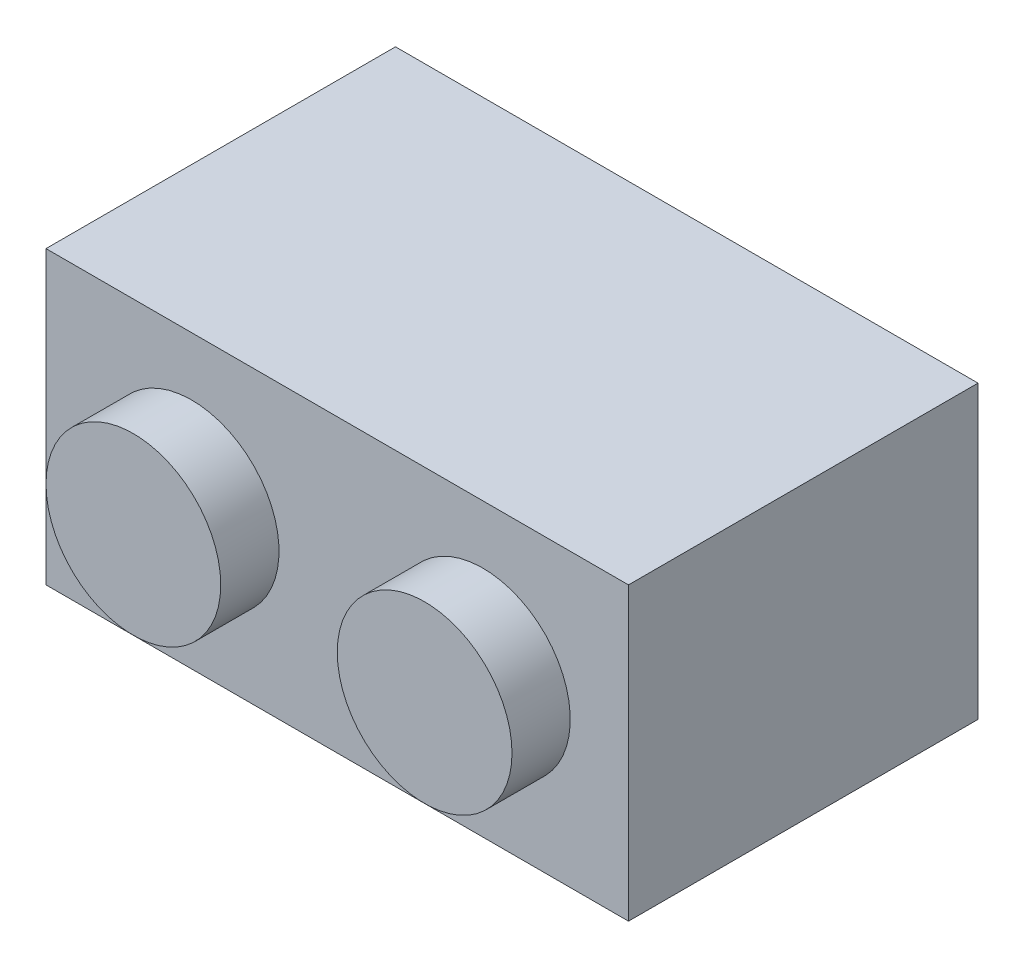
SolidWorks part; units mm, degrees
ref_plane "Front Plane" through (0, 0, 0) normal (0, 0, 1) x (1, 0, 0)
ref_plane "Top Plane" through (0, 0, 0) normal (0, 1, 0) x (1, 0, 0)
ref_plane "Right Plane" through (0, 0, 0) normal (1, 0, 0) x (0, 0, -1)
sketch "Sketch1" plane through (0, 0, 0) normal (0, 0, 1) x (1, 0, 0)
  line L1 (0, 0) -> (15.875, 0)
  line L2 (0, 0) -> (0, 7.9375)
  line L3 (0, 7.9375) -> (15.875, 7.9375)
  line L4 (15.875, 0) -> (15.875, 7.9375)
  dimension "D1" = 7.9375
  dimension "D2" = 15.875
extrude "Boss-Extrude1" add sketch "Sketch1" along normal blind 9.525 contours L3 L4 L1 L2
sketch "Sketch2" plane through (0, 0, 9.525) normal (0, 0, 1) x (1, 0, 0)
  line L0 (0, 7.9375) -> (15.875, 7.9375) construction
  line L1 (0, 0) -> (0, 7.9375) construction
  circle A0 centre (3.9688, 3.9688) radius 2.3813
  dimension "D1" = 4.7625
  dimension "D2" = 3.9688
  dimension "D3" = 3.9688
extrude "Boss-Extrude2" add sketch "Sketch2" along normal blind 1.5875
pattern_linear "LPattern1" count 2 spacing 7.9375 along (1, 0, 0) of "Boss-Extrude2"
shell "Shell3" thickness 1.5875
sketch "Sketch3" plane through (0, 0, 7.9375) normal (0, 0, -1) x (-1, 0, 0)
  line L0 (0, 7.9375) -> (-15.875, 7.9375) construction
  line L1 (-15.875, 0) -> (-15.875, 7.9375) construction
  circle A0 centre (-7.9375, 3.9688) radius 1.5875
  dimension "D1" = 3.175
  dimension "D2" = 3.9688
  dimension "D3" = 7.9375
extrude "Boss-Extrude3" add sketch "Sketch3" along normal blind 7.9375
